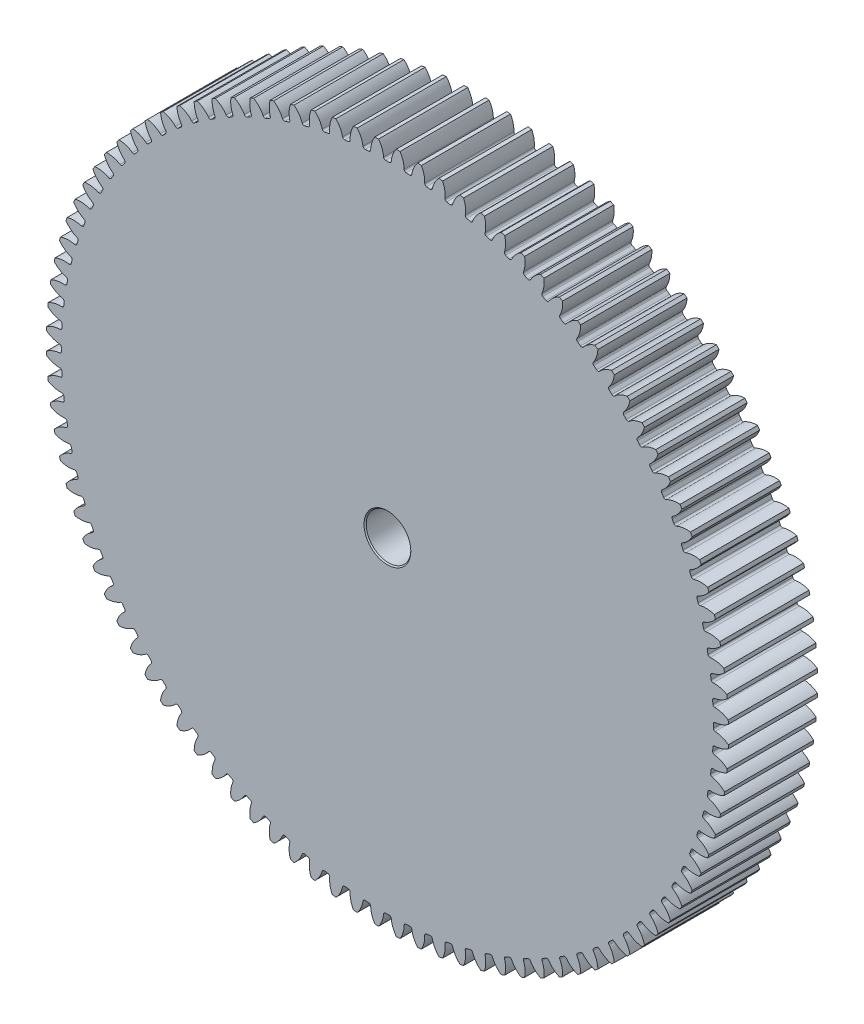
SolidWorks part; units mm, degrees
material "Plain Carbon Steel"
ref_plane "Front" through (0, 0, 0) normal (0, 0, 1) x (1, 0, 0)
ref_plane "Top" through (0, 0, 0) normal (0, 1, 0) x (1, 0, 0)
ref_plane "Right" through (0, 0, 0) normal (1, 0, 0) x (0, 0, -1)
sketch "Sketch1" plane through (0, 0, 0) normal (0, 0, 1) x (1, 0, 0)
  circle A0 centre (0, 0) radius 75
  circle A1 centre (0, 0) radius 76.5
  circle A2 centre (0, 0) radius 73.125
  dimension "D1" = 150
  dimension "D2" = 153
  dimension "D3" = 3.375
extrude "Extrude2" add sketch "Sketch1" along normal mid plane 20 contours A1
sketch "Sketch2" plane through (0, 0, 0) normal (0, 0, 1) x (1, 0, 0)
  line L0 (0, 0) -> (0, 76.5) construction
  line L1 (-1.178, 74.9907) -> (1.178, 74.9907) construction
  line L2 (0, 0) -> (-0.8372, 73.1202) construction
  line L3 (0, 71.7541) -> (-2.0812, 77.4721) construction
  line L4 (0, 0) -> (2.4029, 76.4623) construction
  line L5 (1.178, 74.9907) -> (3.533, 74.9167) construction
  circle A0 centre (0, 0) radius 76.5 construction
  arc A1 (-2.9243, 77.4448) -> (-0.8372, 73.1202) centre (-6.4953, 73.0554) cw
  arc A2 (2.9243, 77.4448) -> (0.8372, 73.1202) centre (6.4953, 73.0554) ccw
  circle A3 centre (0, 0) radius 73.125 construction
  arc A4 (0.8372, 73.1202) -> (-0.8372, 73.1202) centre (0, 0) ccw
  circle A5 centre (0, 0) radius 76.5 construction
  circle A7 centre (0, 0) radius 75 construction
  circle A8 centre (0, 0) radius 77.5
  arc A9 (2.9243, 77.4448) -> (-2.9243, 77.4448) centre (0, 0) ccw
  circle A10 centre (0, 0) radius 47.99 construction
  point P2 (0, 74.9907)
  point P15 (-10.6695, 53.4854)
  dimension "D4" = 95.98
  dimension "D2" = 20
  dimension "D3" = 1.8
  dimension "D1" = 1
extrude "Extrude3" cut sketch "Sketch2" against normal through all both and the other way through all
fillet "Fillet1" radius 0.45 2 edges at (0.8372, 73.1202, 0) (-0.8372, 73.1202, 0)
pattern_circular "CirPattern1" count 100 over 360 about axis through (0, 0, 0) along (0, 0, 1) of "Extrude3", "Fillet1"
sketch "Sketch3" plane through (0, 0, 10) normal (0, 0, 1) x (1, 0, 0)
  circle A0 centre (0, 0) radius 5
  dimension "D1" = 10
extrude "Extrude4" cut sketch "Sketch3" against normal through all both and the other way through all
chamfer "Chamfer1" distance 0.25 angle 45 2 edges at (5, 0, -10) (5, 0, 10)
scale "Scale1" scale about centroid uniform scaling yes scale factor 0.1
equation "\"Moduul\"= 1.5mm'Moduul"
equation "\"Aantal tanden\"= 100'Aantal tanden"
equation "\"D1@Sketch1\"=\"Aantal tanden\" * \"Moduul\""
equation "\"D2@Sketch1\"=(\"Aantal tanden\" + 2 ) * \"Moduul\""
equation "\"D3@Sketch1\"=\"Moduul\" * if( \"Moduul\"=>1.25,2.25,2.4)"
equation "\"D3@Sketch2\"=180 / \"Aantal tanden\""
equation "\"D1@Fillet1\"=0.3 * \"Moduul\""
equation "\"D1@CirPattern1\"=\"Aantal tanden\""
